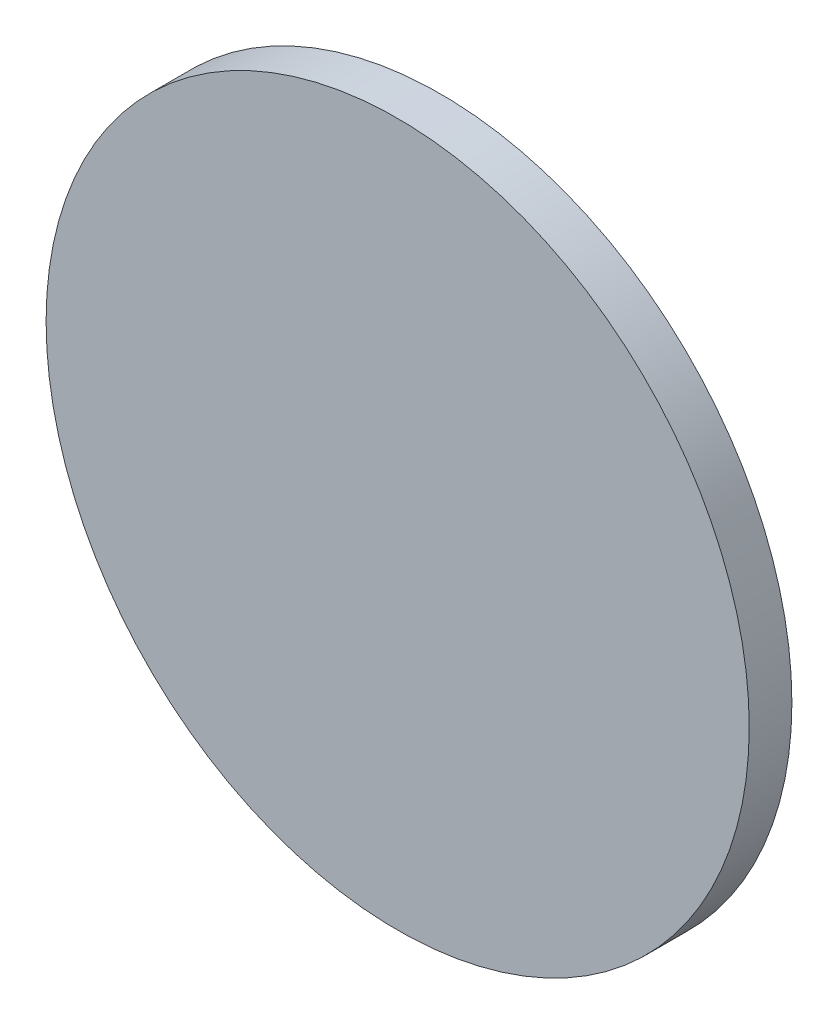
SolidWorks part; units mm, degrees
material "Bismuth"
ref_plane "Front" through (0, 0, 0) normal (0, 0, 1) x (1, 0, 0)
ref_plane "Top" through (0, 0, 0) normal (0, 1, 0) x (1, 0, 0)
ref_plane "Right" through (0, 0, 0) normal (1, 0, 0) x (0, 0, -1)
sketch "Sketch1" plane through (0, 0, 0) normal (0, 0, 1) x (1, 0, 0)
  circle A2 centre (0, 0) radius 75
extrude "Boss-Extrude1" add sketch "Sketch1" along normal blind 9.1 contours A2
